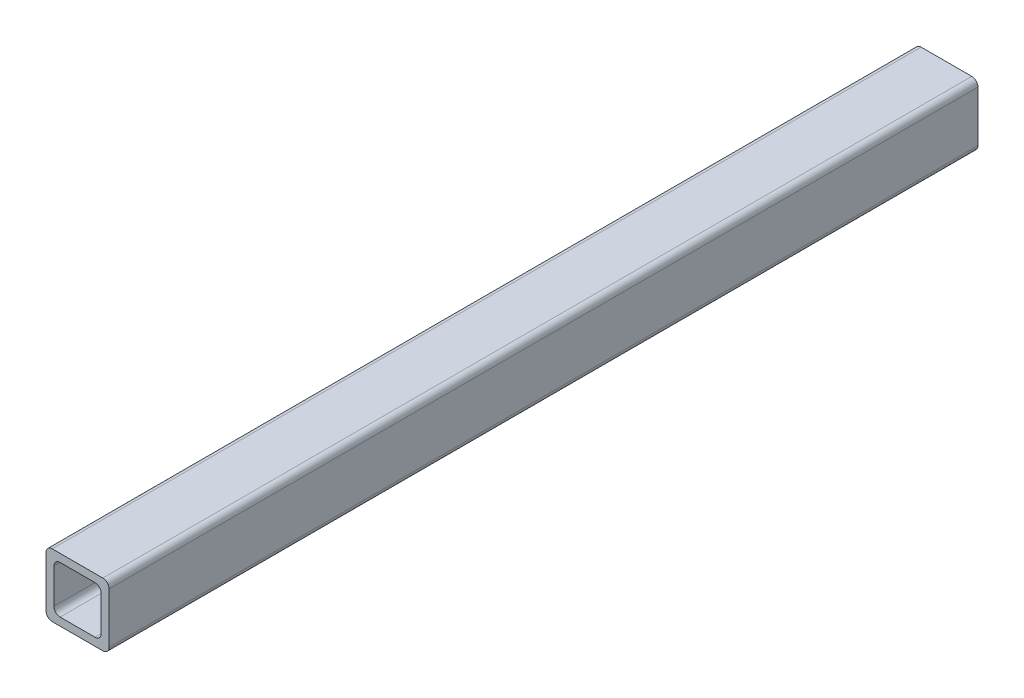
SolidWorks part; units mm, degrees
ref_plane "Alzado" through (0, 0, 0) normal (0, 0, 1) x (1, 0, 0)
ref_plane "Planta" through (0, 0, 0) normal (0, 1, 0) x (1, 0, 0)
ref_plane "Vista lateral" through (0, 0, 0) normal (1, 0, 0) x (0, 0, -1)
sketch "Croquis1" plane through (0, 0, 0) normal (0, 0, 1) x (1, 0, 0)
  line L1 (-7.025, -9.525) -> (7.025, -9.525)
  line L2 (-9.525, -7.025) -> (-9.525, 7.025)
  line L3 (-7.025, 9.525) -> (7.025, 9.525)
  line L4 (9.525, -7.025) -> (9.525, 7.025)
  line L5 (-9.525, -9.525) -> (9.525, 9.525) construction
  line L6 (-9.525, 9.525) -> (9.525, -9.525) construction
  line L7 (-10.2, -12.7) -> (10.2, -12.7)
  line L8 (-12.7, -10.2) -> (-12.7, 10.2)
  line L9 (-10.2, 12.7) -> (10.2, 12.7)
  line L10 (12.7, -10.2) -> (12.7, 10.2)
  line L11 (-12.7, -12.7) -> (12.7, 12.7) construction
  line L12 (-12.7, 12.7) -> (12.7, -12.7) construction
  arc A0 (-7.025, -9.525) -> (-9.525, -7.025) centre (-7.025, -7.025) cw
  arc A1 (7.025, -9.525) -> (9.525, -7.025) centre (7.025, -7.025) ccw
  arc A2 (9.525, 7.025) -> (7.025, 9.525) centre (7.025, 7.025) ccw
  arc A3 (12.7, -10.2) -> (10.2, -12.7) centre (10.2, -10.2) cw
  arc A4 (-10.2, -12.7) -> (-12.7, -10.2) centre (-10.2, -10.2) cw
  arc A5 (12.7, 10.2) -> (10.2, 12.7) centre (10.2, 10.2) ccw
  arc A6 (-9.525, 7.025) -> (-7.025, 9.525) centre (-7.025, 7.025) cw
  arc A7 (-10.2, 12.7) -> (-12.7, 10.2) centre (-10.2, 10.2) ccw
  point P0 (0, 0)
  point P6 (0, 0)
  dimension "D3" = 2.5
  dimension "D1" = 25.4
  dimension "D2" = 3.175
extrude "Saliente-Extruir1" add sketch "Croquis1" along normal blind 350
